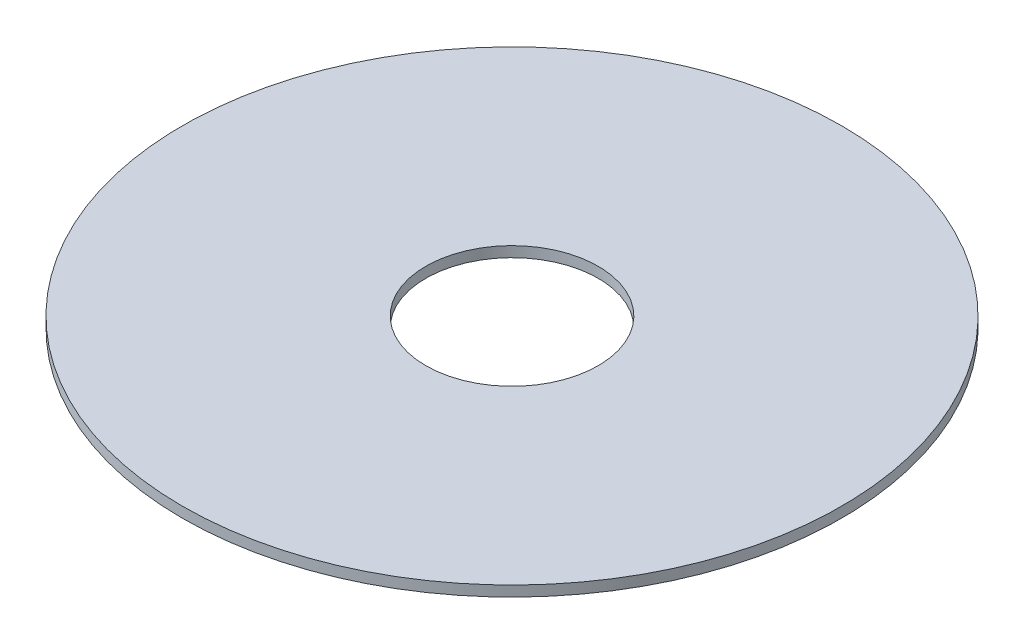
SolidWorks part; units mm, degrees
ref_plane "Front Plane" through (0, 0, 0) normal (0, 0, 1) x (1, 0, 0)
ref_plane "Top Plane" through (0, 0, 0) normal (0, 1, 0) x (1, 0, 0)
ref_plane "Right Plane" through (0, 0, 0) normal (1, 0, 0) x (0, 0, -1)
sketch "Sketch1" plane through (0, 0, 0) normal (0, 1, 0) x (1, 0, 0)
  circle A0 centre (0, 0) radius 53.5344
  circle A1 centre (0, 0) radius 14
extrude "Boss-Extrude1" add sketch "Sketch1" along normal blind 1.7
